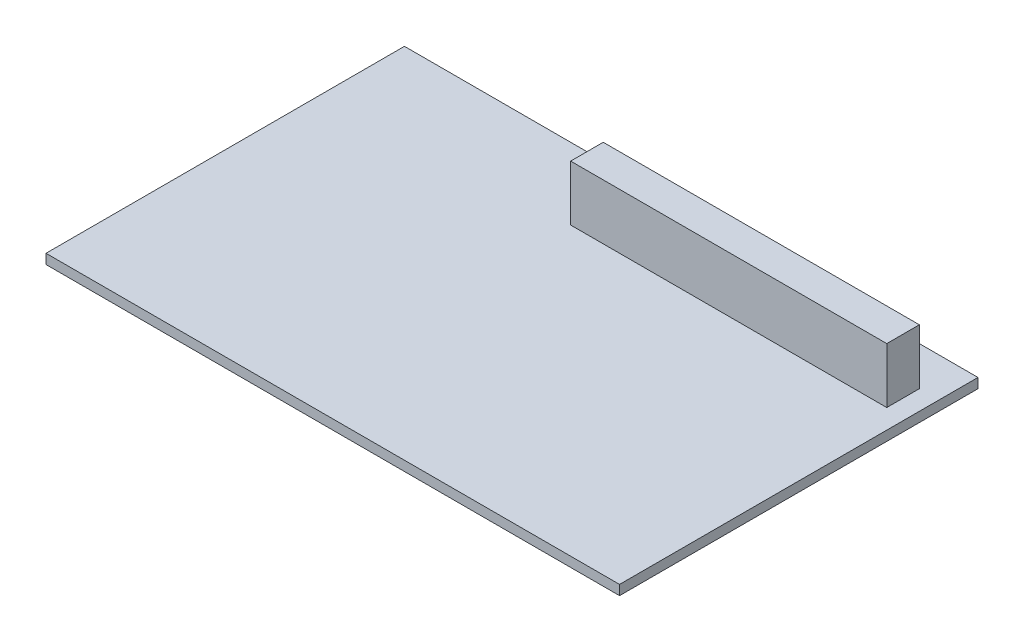
SolidWorks part; units mm, degrees
ref_plane "Płaszczyzna przednia" through (0, 0, 0) normal (0, 0, 1) x (1, 0, 0)
ref_plane "Płaszczyzna górna" through (0, 0, 0) normal (0, 1, 0) x (1, 0, 0)
ref_plane "Płaszczyzna prawa" through (0, 0, 0) normal (1, 0, 0) x (0, 0, -1)
sketch "Szkic1" plane through (0, 0, 0) normal (0, 1, 0) x (1, 0, 0)
  line L1 (-44, -27.5) -> (44, -27.5)
  line L2 (-44, -27.5) -> (-44, 27.5)
  line L3 (-44, 27.5) -> (44, 27.5)
  line L4 (44, -27.5) -> (44, 27.5)
  line L5 (-44, -27.5) -> (44, 27.5) construction
  line L6 (-44, 27.5) -> (44, -27.5) construction
  point P0 (0, 0)
  dimension "D1" = 55
  dimension "D2" = 88
extrude "Dodanie-wyciągnięcie1" add sketch "Szkic1" along normal blind 1.5
sketch "Szkic2" plane through (0, 1.5, 0) normal (0, 1, 0) x (1, 0, 0)
  line L0 (44, -27.5) -> (44, 27.5) construction
  line L1 (-7.5, 16.5) -> (41, 16.5)
  line L2 (-7.5, 16.5) -> (-7.5, 21.5)
  line L3 (-7.5, 21.5) -> (41, 21.5)
  line L4 (41, 16.5) -> (41, 21.5)
  line L5 (44, 27.5) -> (-44, 27.5) construction
  dimension "D1" = 5
  dimension "D2" = 48.5
  dimension "D3" = 3
  dimension "D4" = 6
extrude "Dodanie-wyciągnięcie2" add sketch "Szkic2" along normal blind 8.5
